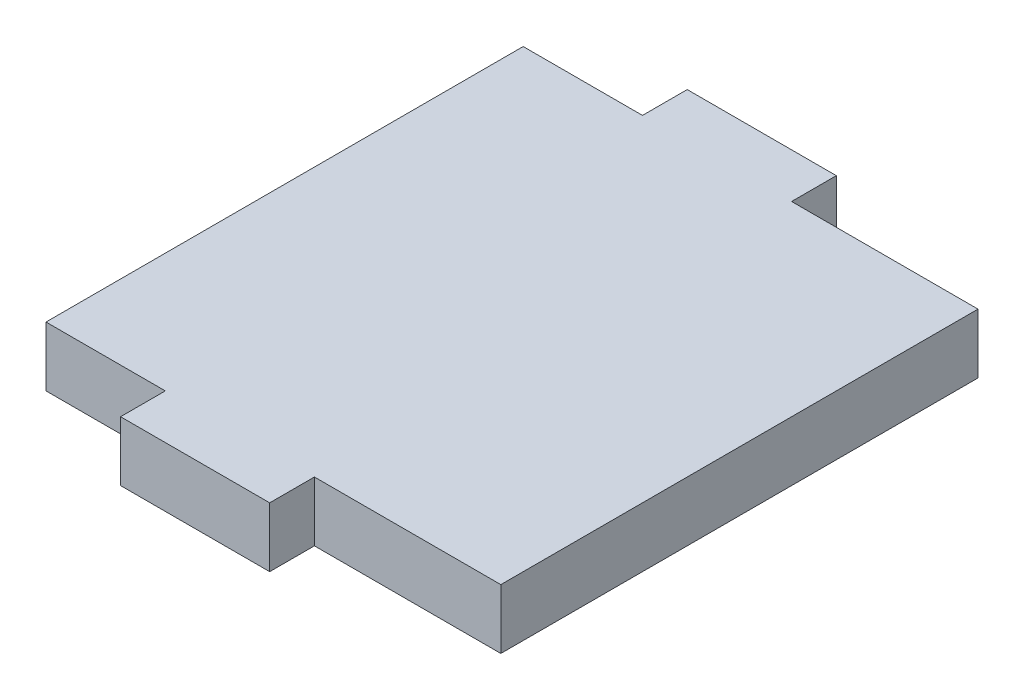
SolidWorks part; units mm, degrees
material "Acier S235"
ref_plane "Plan de face" through (0, 0, 0) normal (0, 0, 1) x (1, 0, 0)
ref_plane "Plan de dessus" through (0, 0, 0) normal (0, 1, 0) x (1, 0, 0)
ref_plane "Plan de droite" through (0, 0, 0) normal (1, 0, 0) x (0, 0, -1)
sketch "Esquisse1" plane through (0, 0, 0) normal (0, 1, 0) x (1, 0, 0)
  line L0 (2.75, -19) -> (-7.25, -19)
  line L1 (-15.25, -19) -> (15.25, -19) construction
  line L2 (-15.25, -19) -> (-15.25, 19) construction
  line L3 (-15.25, 19) -> (15.25, 19) construction
  line L4 (15.25, -19) -> (15.25, 19) construction
  line L5 (-7.25, -19) -> (-7.25, -16)
  line L6 (-7.25, -16) -> (-15.25, -16)
  line L7 (-15.25, -16) -> (-15.25, 16)
  line L8 (-15.25, 16) -> (-7.25, 16)
  line L9 (-7.25, 16) -> (-7.25, 19)
  line L10 (-7.25, 19) -> (2.75, 19)
  line L11 (2.75, 19) -> (2.75, 16)
  line L12 (2.75, 16) -> (15.25, 16)
  line L13 (15.25, 16) -> (15.25, -16)
  line L14 (15.25, -16) -> (2.75, -16)
  line L15 (2.75, -16) -> (2.75, -19)
  point P0 (0, 0)
  point P6 (0, 19)
  point P7 (15.25, 0)
  dimension "D1" = 10
  dimension "D2" = 38
  dimension "D3" = 3
  dimension "D4" = 8
  dimension "D5" = 12.5
extrude "Boss.-Extru.1" add sketch "Esquisse1" along normal blind 4
